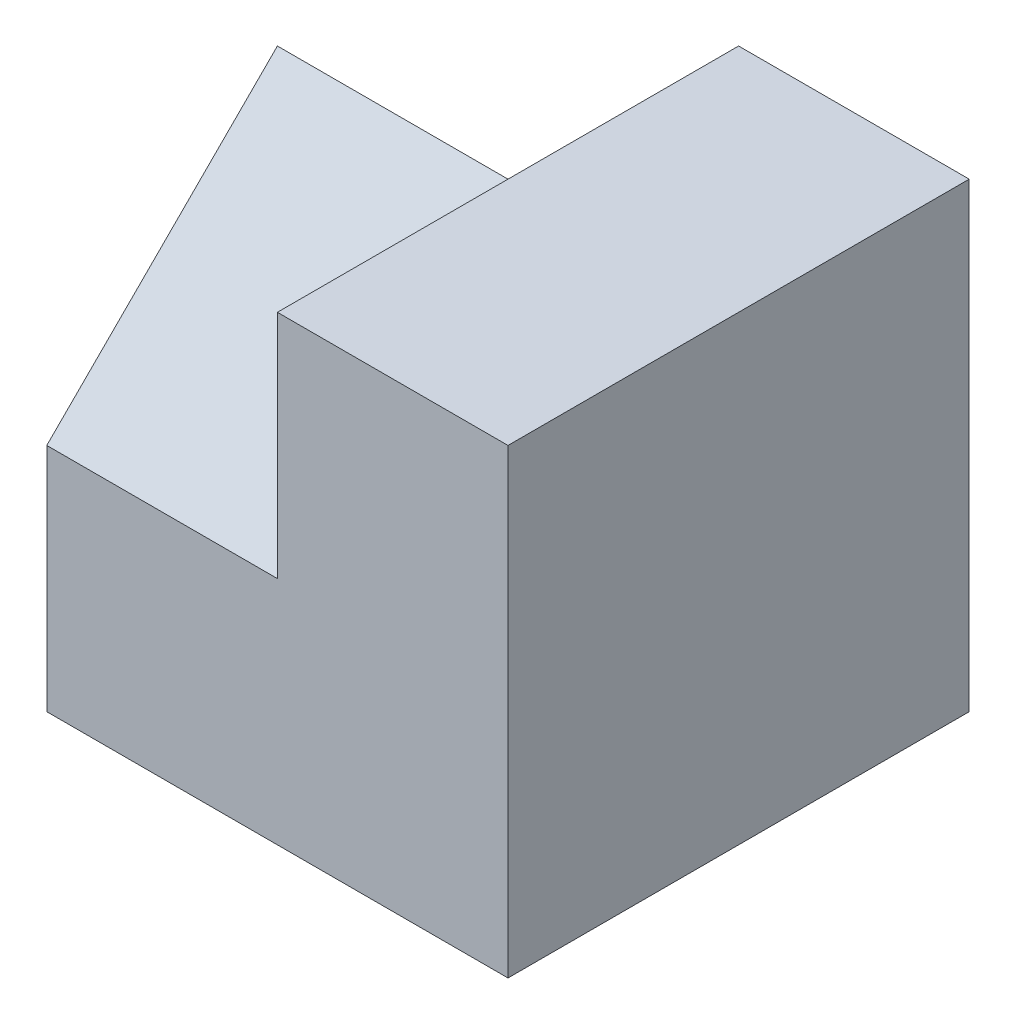
SolidWorks part; units mm, degrees
ref_plane "Front" through (0, 0, 0) normal (0, 0, 1) x (1, 0, 0)
ref_plane "Top" through (0, 0, 0) normal (0, 1, 0) x (1, 0, 0)
ref_plane "Right" through (0, 0, 0) normal (1, 0, 0) x (0, 0, -1)
sketch "Sketch1" plane through (0, 0, 0) normal (0, 1, 0) x (1, 0, 0)
  line L1 (-2, -2) -> (2, -2)
  line L2 (-2, -2) -> (-2, 2)
  line L3 (-2, 2) -> (2, 2)
  line L4 (2, -2) -> (2, 2)
  line L5 (-2, -2) -> (2, 2) construction
  line L6 (-2, 2) -> (2, -2) construction
  point P0 (0, 0)
  dimension "D1" = 4
  dimension "D2" = 4
extrude "Boss-Extrude1" add sketch "Sketch1" along normal blind 4
sketch "Sketch2" plane through (-2, 0, 0) normal (-1, 0, 0) x (0, 0, 1)
  line L0 (2, 2) -> (0, 4)
  line L1 (2, 4) -> (2, 0) construction
  line L2 (-2, 4) -> (2, 4) construction
  line L3 (0, 4) -> (-2, 2)
  line L4 (-2, 4) -> (-2, 0) construction
  line L9 (-2, 0) -> (2, 0)
  line L10 (2, 0) -> (2, 4)
  line L11 (2, 4) -> (-2, 4)
  line L12 (-2, 4) -> (-2, 0)
  line L13 (-2, 0) -> (2, 0)
  line L14 (2, 0) -> (2, 4)
  line L15 (2, 4) -> (-2, 4)
  line L16 (-2, 4) -> (-2, 0)
  line M6 (2, 0) -> (2, 4)
  line M7 (2, 4) -> (-2, 4)
  line M8 (-2, 4) -> (-2, 0)
  dimension "D1" = 0
extrude "Cut-Extrude1" cut sketch "Sketch2" against normal blind 2 contours L3 M7 M8 | L0 M6 M7
